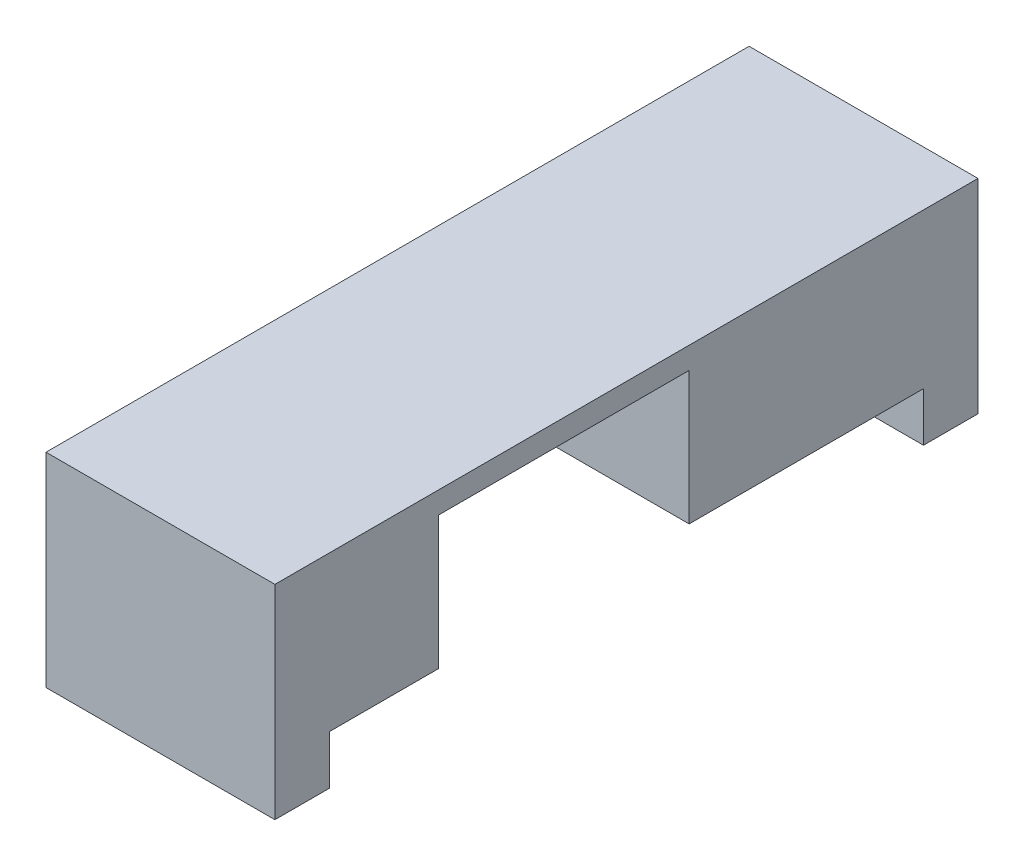
SolidWorks part; units mm, degrees
ref_plane "Front Plane" through (0, 0, 0) normal (0, 0, 1) x (1, 0, 0)
ref_plane "Top Plane" through (0, 0, 0) normal (0, 1, 0) x (1, 0, 0)
ref_plane "Right Plane" through (0, 0, 0) normal (1, 0, 0) x (0, 0, -1)
sketch "Sketch1" plane through (0, 0, 0) normal (0, 1, 0) x (1, 0, 0)
  line L1 (0, 0) -> (-21, 0)
  line L2 (0, 0) -> (0, -64.5)
  line L3 (0, -64.5) -> (-21, -64.5)
  line L4 (-21, 0) -> (-21, -64.5)
  dimension "D1" = 21
  dimension "D2" = 64.5
extrude "Boss-Extrude1" add sketch "Sketch1" along normal blind 18.7
sketch "Sketch2" plane through (0, 0, 0) normal (1, 0, 0) x (0, 0, -1)
  line L0 (-64.5, 0) -> (0, 0) construction
  line L1 (-59.5, 0) -> (-5, 0)
  line L2 (-59.5, 0) -> (-59.5, 4.5)
  line L3 (-59.5, 4.5) -> (-49.5, 4.5)
  line L4 (-5, 0) -> (-5, 4.5)
  line L5 (-64.5, 18.7) -> (-64.5, 0) construction
  line L6 (0, 18.7) -> (0, 0) construction
  line L7 (-26.5, 4.5) -> (-5, 4.5)
  line L9 (-49.5, 4.5) -> (-49.5, 16.7)
  line L10 (-49.5, 16.7) -> (-26.5, 16.7)
  line L11 (-26.5, 4.5) -> (-26.5, 16.7)
  dimension "D1" = 5
  dimension "D2" = 5
  dimension "D3" = 4.5
  dimension "D4" = 15
  dimension "D5" = 23
  dimension "D6" = 12.2
extrude "Cut-Extrude1" cut sketch "Sketch2" against normal through all
sketch "Sketch3" plane through (0, 0, 59.5) normal (0, 0, -1) x (-1, 0, 0)
  line L0 (21, 0) -> (0, 0) construction
  line L1 (12.3, 0) -> (15.5, 0)
  line L2 (12.3, 0) -> (12.3, 4.5)
  line L3 (12.3, 4.5) -> (15.5, 4.5)
  line L4 (15.5, 0) -> (15.5, 4.5)
  line L5 (0, 4.5) -> (0, 0) construction
  line L6 (21, 4.5) -> (0, 4.5) construction
  dimension "D1" = 12.3
  dimension "D2" = 3.2
extrude "Cut-Extrude2" cut sketch "Sketch3" against normal blind 3
